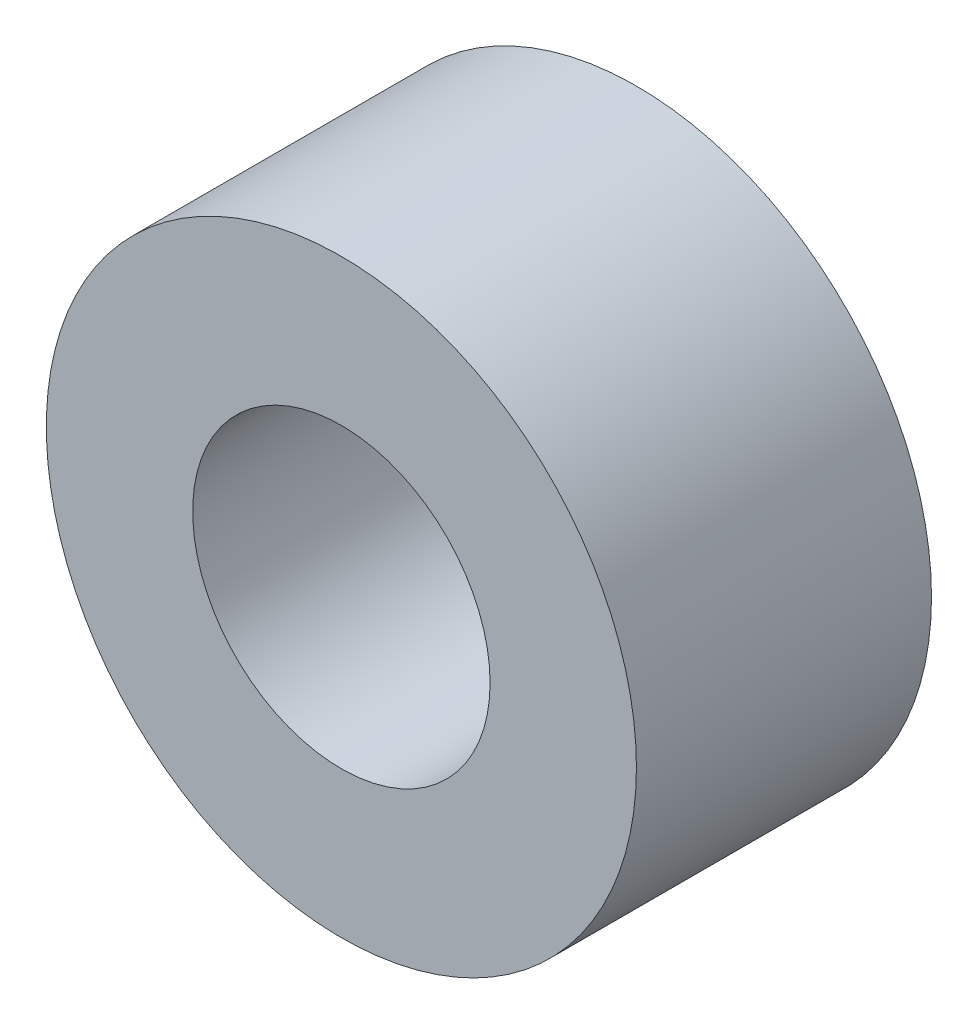
SolidWorks part; units mm, degrees
ref_plane "Front Plane" through (0, 0, 0) normal (0, 0, 1) x (1, 0, 0)
ref_plane "Top Plane" through (0, 0, 0) normal (0, 1, 0) x (1, 0, 0)
ref_plane "Right Plane" through (0, 0, 0) normal (1, 0, 0) x (0, 0, -1)
sketch "Sketch1" plane through (0, 0, 0) normal (0, 0, 1) x (1, 0, 0)
  line L0 (0, 3.2004) -> (0, 6.35) construction
  line L1 (0, -3.2004) -> (0, -6.35) construction
  circle A0 centre (0, 0) radius 6.35
  circle A1 centre (0, 0) radius 3.2004
  dimension "OD" = 12.7
  dimension "ID" = 6.4008
sketch "Sketch2" plane through (0, 0, 0) normal (1, 0, 0) x (0, 0, -1)
  line L0 (-3.175, 3.2004) -> (3.175, 3.2004) construction
  line L1 (-3.175, -3.2004) -> (3.175, -3.2004) construction
  line L2 (-3.175, -6.35) -> (3.175, -6.35) construction
  line L3 (-3.175, 6.35) -> (3.175, 6.35) construction
  dimension "Length" = 6.35
extrude "Extrude1" add sketch "Sketch1" along normal up to vertex (3.175 mm away) and the other way up to vertex (3.175 mm away) up to point (0, 3.2004, 3.175) other way up to point (0, 3.2004, -3.175)
sketch "Sketch3" plane through (0, 0, 3.175) normal (0, 0, 1) x (1, 0, 0)
  circle A0 centre (0, 0) radius 3.2004 construction
  circle A3 centre (0, 0) radius 3.2004
  point P3 (-3.2004, 0)
